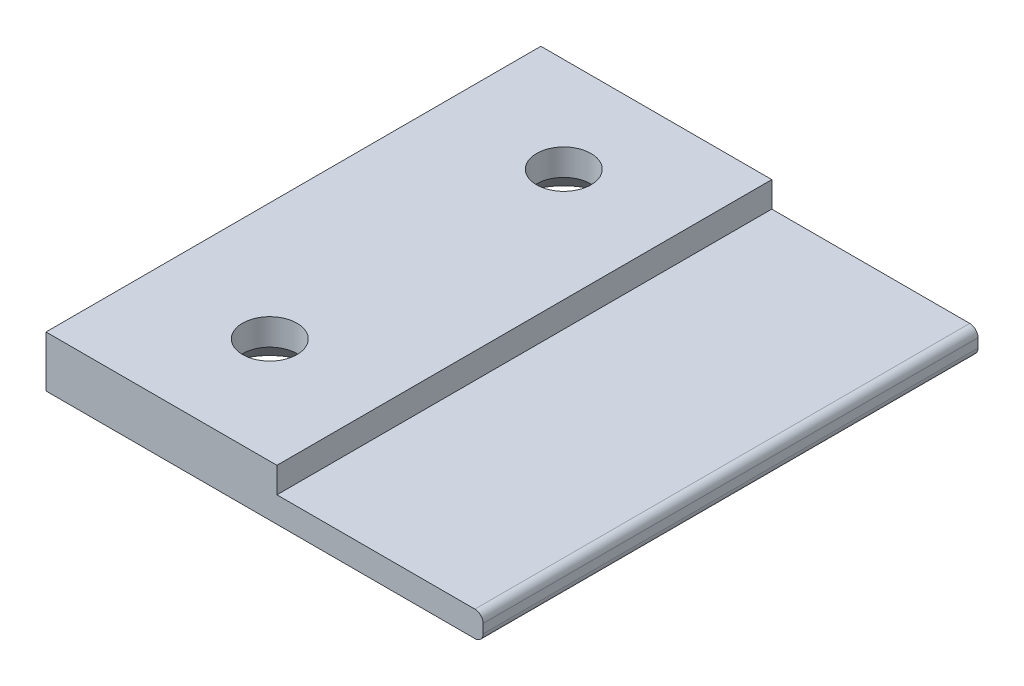
SolidWorks part; units mm, degrees
material "Plastique personnalisé"
ref_plane "Plan de face" through (0, 0, 0) normal (0, 0, 1) x (1, 0, 0)
ref_plane "Plan de dessus" through (0, 0, 0) normal (0, 1, 0) x (1, 0, 0)
ref_plane "Plan de droite" through (0, 0, 0) normal (1, 0, 0) x (0, 0, -1)
sketch "Esquisse1" plane through (0, 0, 0) normal (0, 0, 1) x (1, 0, 0)
  line L0 (0, 0) -> (28, 0)
  line L1 (28, 0) -> (28, -3.1)
  line L2 (0, -3.1) -> (53, -3.1) construction
  line L3 (28, -3.1) -> (53, -3.1)
  line L4 (53, -3.1) -> (53, -6.2)
  line L5 (53, -6.2) -> (0, -6.2)
  line L6 (0, -6.2) -> (0, 0)
  dimension "D1" = 28
  dimension "D2" = 3.1
  dimension "D3" = 53
  dimension "D4" = 3.1
extrude "Boss.-Extru.1" add sketch "Esquisse1" along normal blind 60
fillet "Congé1" radius 1 2 edges at (53, -3.1, 30) (53, -6.2, 30)
hole_wizard "Fraisage pour vis à tête fraisée M62" positions "Esquisse4" profile "Esquisse5" countersink size "M6" standard "ISO"
sketch "Esquisse4" plane through (0, -6.2, 0) normal (0, -1, 0) x (-1, 0, 0)
  point P0 (-14.2938, -11.5151)
  point P2 (-14.2938, -47.1589)
sketch "Esquisse5" plane through (14.2938, -6.2, 11.5151) normal (1, 0, 0) x (0, 0, -1)
  line L0 (0, 0) -> (0, 9.9828)
  line L1 (0, 9.9828) -> (3.3, 8)
  line L2 (3.3, 8) -> (3.3, 3)
  line L3 (3.3, 3) -> (6.3, 0)
  line L5 (6.3, 0) -> (0, 0)
  line L6 (-3.3, 3) -> (-6.3, 0) construction
  line L10 (0, 9.9828) -> (-3.3, 8) construction
  line L11 (0, -6.35) -> (0, 107.95) construction
  dimension "Diamètre du perçage" = 6.6
  dimension "Profondeur du perçage" = 8
  dimension "Diamètre du fraisage entrant" = 12.6
  dimension "Angle du fraisage entrant" = 90
  dimension "Angle de pointe" = 118
